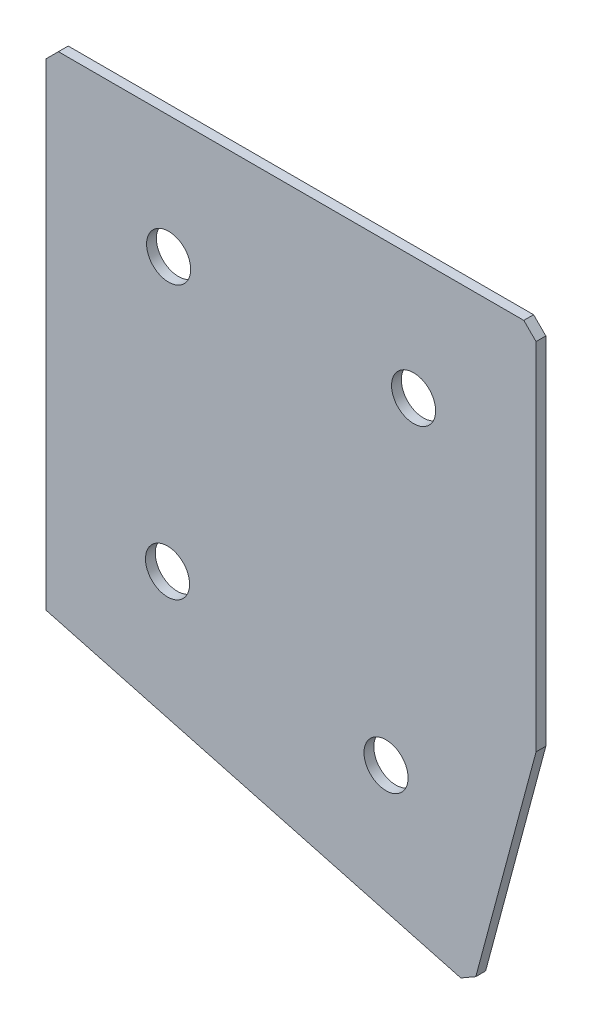
SolidWorks part; units mm, degrees
material "Простая углеродистая сталь"
ref_plane "Спереди" through (0, 0, 0) normal (0, 0, 1) x (1, 0, 0)
ref_plane "Сверху" through (0, 0, 0) normal (0, 1, 0) x (1, 0, 0)
ref_plane "Справа" through (0, 0, 0) normal (1, 0, 0) x (0, 0, -1)
sketch "Эскиз3" plane through (0, 0, 0) normal (0, 0, -1) x (1, 0, 0)
  line L0 (0, 0) -> (100, 0)
  line L1 (100, 0) -> (100, 75.0311)
  line L2 (0, 0) -> (0, 100)
  line L3 (0, 100) -> (87.059, 123.3274)
  line L4 (87.059, 123.3274) -> (100, 75.0311)
  dimension "D1" = 100
  dimension "D2" = 100
  dimension "D3" = 50
  dimension "D4" = 15
  dimension "D5" = 75.0311
extrude "Бобышка-Вытянуть1" add sketch "Эскиз3" along normal blind 2
hole_wizard "Отверстие с зазором M81" positions "Эскиз4" profile "Эскиз5" hole size "M8" standard "DIN" end condition through all
sketch "Эскиз4" plane through (0, 0, -2) normal (0, 0, -1) x (1, 0, 0)
  line L0 (21.4436, 82.7627) -> (62.2804, 93.7049) construction
  line L2 (87.059, 123.3274) -> (0, 100) construction
  line L5 (0, 0) -> (100, 0) construction
  line L6 (0, 100) -> (0, 0) construction
  line L7 (100, 0) -> (100, 75.0311) construction
  line L8 (100, 75.0311) -> (87.059, 123.3274) construction
  line L9 (21.4436, 82.7627) -> (0, 77.0169) construction
  line L10 (25, 25) -> (75, 25) construction
  line L12 (24.7762, 80.7569) -> (69.3814, 92.7088) construction
  line L13 (21.4436, 82.7627) -> (22.1682, 80.0581) construction
  line L14 (22.1682, 80.0581) -> (24.7762, 80.7569) construction
  point P31 (24.7762, 80.7569)
  point P33 (69.3814, 92.7088)
  point P35 (25, 25)
  point P37 (75, 25)
  dimension "D2" = 22.2
  dimension "D6" = 22.2
  dimension "D9" = 25
  dimension "D10" = 25
  dimension "D11" = 25
  dimension "D12" = 25
  dimension "D13" = 25
  dimension "D14" = 2.7
sketch "Эскиз5" plane through (75, -25, -2) normal (1, 0, 0) x (0, 1, 0)
  line L0 (0, 0) -> (0, 2)
  line L1 (0, 2) -> (4.5, 2)
  line L2 (4.5, 2) -> (4.5, 0)
  line L5 (4.5, 0) -> (0, 0)
  line L11 (0, -6.35) -> (0, 107.95) construction
  dimension "Диаметр сквозного отверстия" = 9
  dimension "Глубина сквозного отверстия" = 2
chamfer "Фаска1" distance 2.5 distance2 2.5 3 edges at (87.059, -123.3274, -1) (100, 0, -1) (0, 0, -1)
